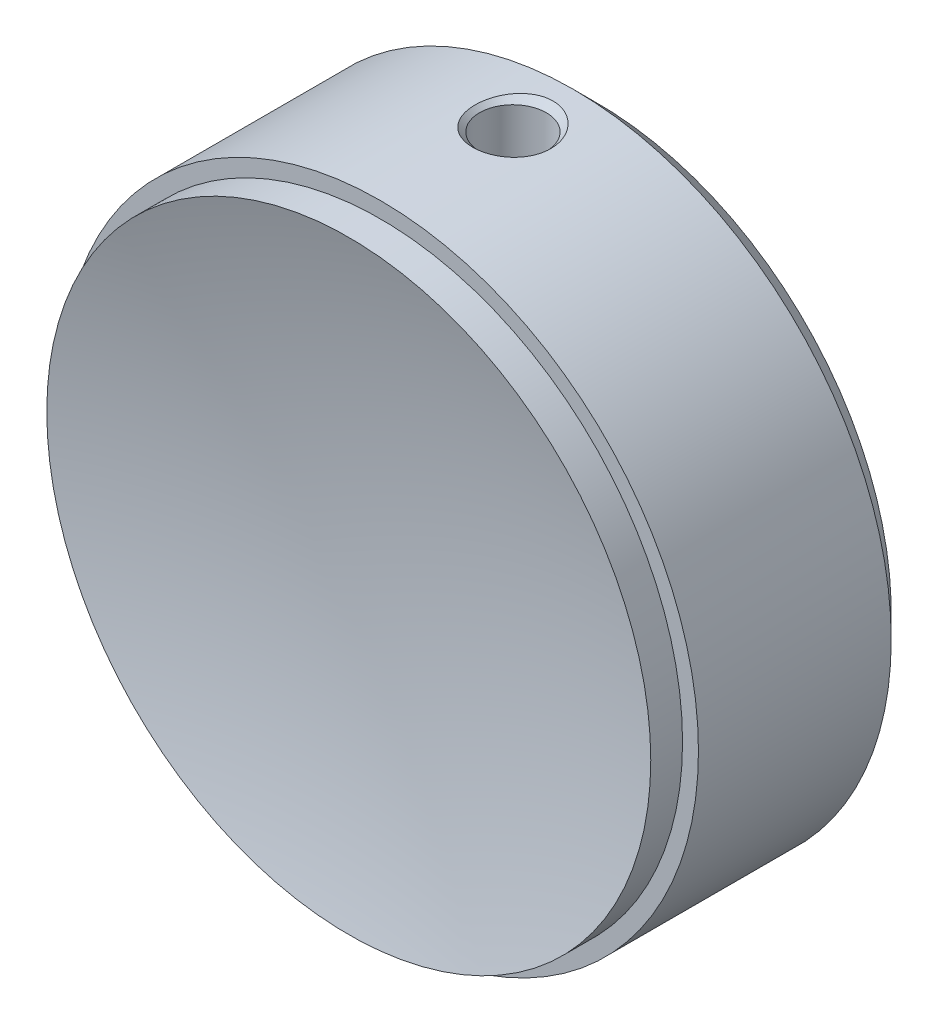
SolidWorks part; units mm, degrees
ref_plane "Front Plane" through (0, 0, 0) normal (0, 0, 1) x (1, 0, 0)
ref_plane "Top Plane" through (0, 0, 0) normal (0, 1, 0) x (1, 0, 0)
ref_plane "Right Plane" through (0, 0, 0) normal (1, 0, 0) x (0, 0, -1)
sketch "Sketch1" plane through (0, 0, 0) normal (0, 1, 0) x (1, 0, 0)
  line L0 (0, 56.5285) -> (0, -333.4547) construction
  line L1 (-6.5, 0) -> (-18.5, 0)
  line L2 (-18.5, 0) -> (-20, -1.5)
  line L3 (-20, -1.5) -> (-20, -13.6279)
  line L4 (-20, -13.6279) -> (-19, -13.6279)
  line L5 (-19, -13.6279) -> (-19, -15.6279)
  line L6 (0, -13) -> (0, -6.5)
  circle A0 centre (0, 0) radius 6.5
  circle A1 centre (0, -83) radius 70
  dimension "D2" = 140
  dimension "D3" = 83
  dimension "D5" = 13
  dimension "D1" = 20
  dimension "D4" = 225
  dimension "D6" = 1.5
  dimension "D7" = 1
  dimension "D8" = 2
revolve "Revolve1" add sketch "Sketch1" angle 360 about L0
sketch "Sketch2" plane through (0, 0, 0) normal (0, 0, -1) x (-1, 0, 0)
  line L0 (0, 0) -> (0, -19.0991) construction
  line L1 (0, 0) -> (-13.7548, 7.9413) construction
  line L2 (0, 0) -> (13.9706, 8.0659) construction
  circle A0 centre (0, 0) radius 10.795 construction
  dimension "D1" = 21.59
  dimension "D2" = 120
  dimension "D3" = 120
hole_wizard "M3 Tapped Hole1" positions "Sketch3" profile "Sketch4" tap size "M3" standard "ISO"
sketch "Sketch3" plane through (0, 0, 0) normal (0, 0, -1) x (-1, 0, 0)
  line L0 (0, 0) -> (0, -19.0991) construction
  line L1 (0, 0) -> (-13.7548, 7.9413) construction
  line L2 (0, 0) -> (13.9706, 8.0659) construction
  circle A0 centre (0, 0) radius 10.795 construction
  point P0 (0, -10.795)
  point P6 (-9.3487, 5.3975)
  point P10 (9.3487, 5.3975)
sketch "Sketch4" plane through (0, -10.795, 0) normal (1, 0, 0) x (0, 1, 0)
  line L0 (0, 0) -> (0, 8.2511)
  line L1 (0, 8.2511) -> (1.25, 7.5)
  line L2 (1.25, 7.5) -> (1.25, 0)
  line L5 (1.25, 0) -> (0, 0)
  line L10 (0, 8.2511) -> (-1.25, 7.5) construction
  line L11 (0, -6.35) -> (0, 107.95) construction
  dimension "Tap Drill Dia." = 2.5
  dimension "Tap Drill Depth" = 7.5
  dimension "Drill Angle" = 118
cosmetic thread "Hole Thread1" parameters "D1"=6, "D2"=3
cosmetic thread "Hole Thread2" parameters "D1"=6, "D2"=3
cosmetic thread "Hole Thread3" parameters "D1"=6, "D2"=3
ref_plane "Plane1" through (0, 20, 0) normal (0, 1, 0) x (1, 0, 0)
sketch "Sketch5" plane through (0, 20, 0) normal (0, 1, 0) x (1, 0, 0)
  line L0 (0, 5.3207) -> (0, -21.1896) construction
  line L1 (-15.6368, -5.3) -> (12.6708, -5.3) construction
  line L2 (18.5, 0) -> (-18.5, 0) construction
  dimension "D1" = 5.3
hole_wizard "M5 Tapped Hole1" positions "Sketch6" profile "Sketch7" tap size "M5" standard "ISO"
sketch "Sketch6" plane through (0, 20, 0) normal (0, 1, 0) x (1, 0, 0)
  line L0 (0, 5.3207) -> (0, -21.1896) construction
  line L1 (-15.6368, -5.3) -> (12.6708, -5.3) construction
  point P0 (0, -5.3)
sketch "Sketch7" plane through (0, 20, 5.3) normal (1, 0, 0) x (0, 0, 1)
  line L0 (0, 0) -> (0, 13.6618)
  line L1 (0, 13.6618) -> (2.1, 12.4)
  line L2 (2.1, 12.4) -> (2.1, 0.425)
  line L3 (2.1, 0.425) -> (2.525, 0)
  line L5 (2.525, 0) -> (0, 0)
  line L6 (-2.1, 0.425) -> (-2.525, 0) construction
  line L10 (0, 13.6618) -> (-2.1, 12.4) construction
  line L11 (0, -6.35) -> (0, 107.95) construction
  dimension "Tap Drill Dia." = 4.2
  dimension "Tap Drill Depth" = 12.4
  dimension "Near C'Sink Dia." = 5.05
  dimension "Near C'Sink Angle" = 90
  dimension "Drill Angle" = 118
cosmetic thread "Hole Thread4" parameters "D1"=10, "D2"=5
